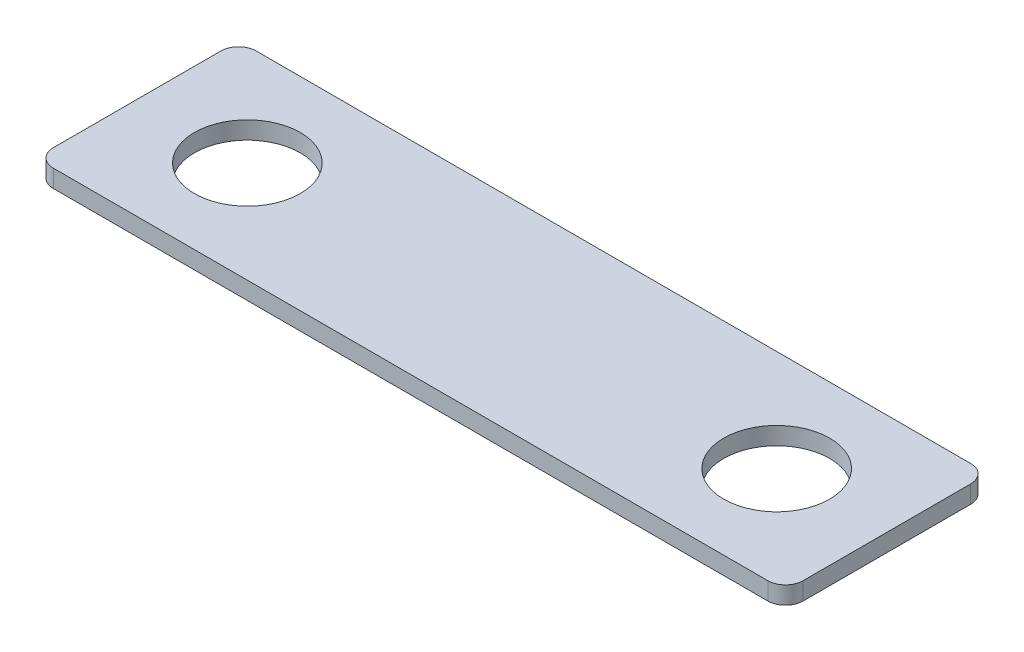
SolidWorks part; units mm, degrees
material "Медь"
ref_plane "Front" through (0, 0, 0) normal (0, 0, 1) x (1, 0, 0)
ref_plane "Top" through (0, 0, 0) normal (0, 1, 0) x (1, 0, 0)
ref_plane "Right" through (0, 0, 0) normal (1, 0, 0) x (0, 0, -1)
sketch "Эскиз1" plane through (0, 0, 0) normal (0, 1, 0) x (1, 0, 0)
  line L0 (0, 6) -> (0, 11.5) construction
  line L1 (40.5, -11.5) -> (-40.5, -11.5)
  line L2 (42.5, -9.5) -> (42.5, 9.5)
  line L3 (40.5, 11.5) -> (-40.5, 11.5)
  line L4 (-42.5, -9.5) -> (-42.5, 9.5)
  line L5 (42.5, -11.5) -> (0, 0) construction
  line L6 (42.5, 11.5) -> (0, 0) construction
  line L9 (0, 0) -> (-42.5, 11.5) construction
  line L10 (0, 0) -> (-42.5, -11.5) construction
  arc A0 (-30, 6) -> (-30, -6) centre (-30, 0) ccw
  arc A1 (30, 6) -> (30, -6) centre (30, 0) cw
  arc A2 (40.5, -11.5) -> (42.5, -9.5) centre (40.5, -9.5) ccw
  arc A3 (42.5, 9.5) -> (40.5, 11.5) centre (40.5, 9.5) ccw
  arc A4 (-40.5, -11.5) -> (-42.5, -9.5) centre (-40.5, -9.5) cw
  arc A5 (-40.5, 11.5) -> (-42.5, 9.5) centre (-40.5, 9.5) ccw
  arc A6 (-30, 6) -> (-30, -6) centre (-30, 0) cw
  arc A7 (30, 6) -> (30, -6) centre (30, 0) ccw
  point P0 (0, 0)
  dimension "D3" = 12
  dimension "D6" = 2
  dimension "D1" = 23
  dimension "D2" = 85
  dimension "D4" = 30
  dimension "D5" = 11.5
extrude "Бобышка-Вытянуть1" add sketch "Эскиз1" along normal blind 2
